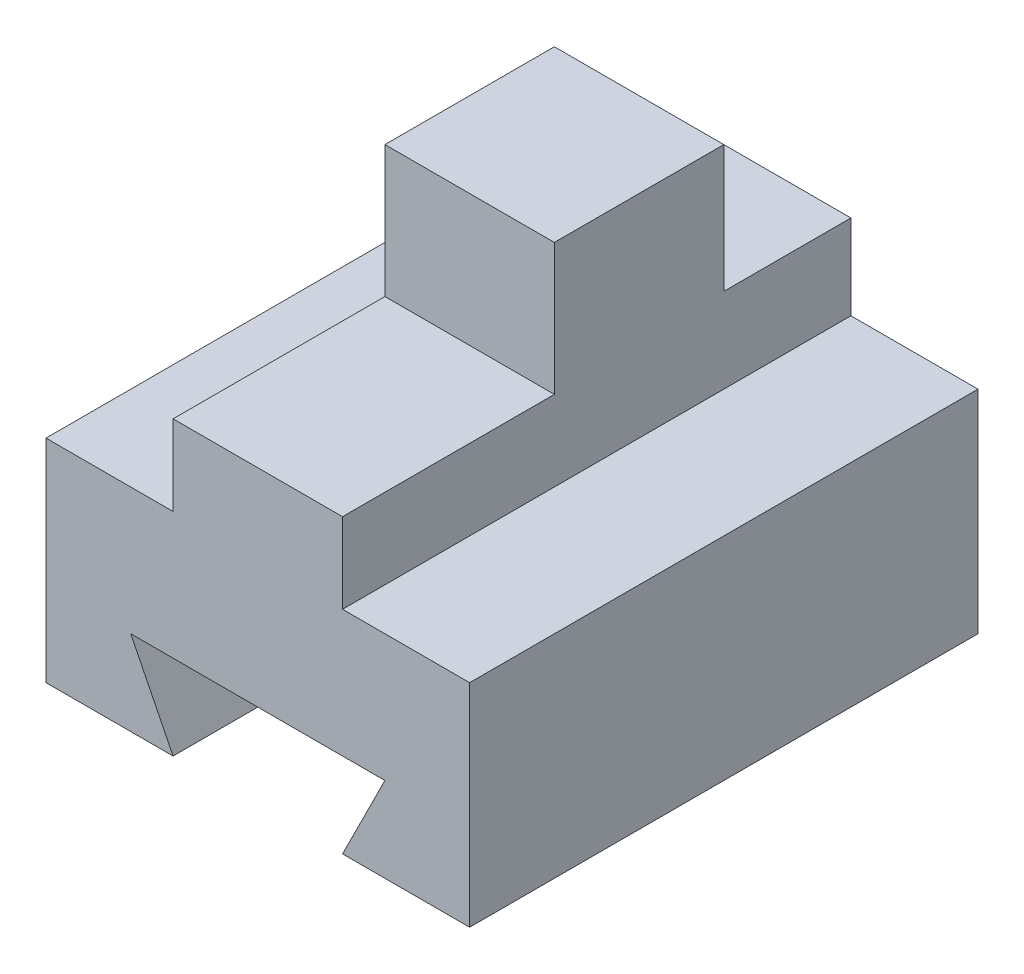
SolidWorks part; units mm, degrees
ref_plane "Ön Düzlem" through (0, 0, 0) normal (0, 0, 1) x (1, 0, 0)
ref_plane "Üst Düzlem" through (0, 0, 0) normal (0, 1, 0) x (1, 0, 0)
ref_plane "Sağ Düzlem" through (0, 0, 0) normal (1, 0, 0) x (0, 0, -1)
sketch "Çizim1" plane through (0, 0, 0) normal (0, 0, 1) x (1, 0, 0)
  line L1 (-38.103, 22.3684) -> (11.897, 22.3684)
  line L2 (-38.103, 22.3684) -> (-38.103, -27.6316)
  line L3 (-38.103, -27.6316) -> (11.897, -27.6316)
  line L4 (11.897, 22.3684) -> (11.897, -27.6316)
  dimension "D1" = 50
  dimension "D2" = 50
extrude "Yükseklik-Ekstrüzyon1" add sketch "Çizim1" along normal blind 60
sketch "Çizim2" plane through (0, 0, 60) normal (0, 0, 1) x (1, 0, 0)
  line L1 (-28.103, -17.6316) -> (1.897, -17.6316)
  line L2 (1.897, -17.6316) -> (-3.103, -27.6316)
  line L3 (-3.103, -27.6316) -> (-23.103, -27.6316)
  line L4 (-23.103, -27.6316) -> (-28.103, -17.6316)
extrude "Kes-Ekstrüzyon1" cut sketch "Çizim2" against normal blind 60
sketch "Çizim3" plane through (0, 0, 60) normal (0, 0, 1) x (1, 0, 0)
  line L1 (11.897, -27.6316) -> (11.897, 22.3684) construction
  line L2 (11.897, -2.6316) -> (-3.103, -2.6316)
  line L3 (-3.103, -2.6316) -> (-3.103, 22.3684)
  line L4 (11.897, 22.3684) -> (-38.103, 22.3684) construction
  line L5 (-3.103, 22.3684) -> (11.897, 22.3684)
  line L6 (11.897, 22.3684) -> (11.897, -2.6316)
  line L7 (-38.103, 22.3684) -> (-38.103, -27.6316) construction
  line L8 (-38.103, -2.6316) -> (-23.103, -2.6316)
  line L9 (-23.103, -2.6316) -> (-23.103, 22.3684)
  line L10 (-23.103, 22.3684) -> (-38.103, 22.3684)
  line L11 (-38.103, 22.3684) -> (-38.103, -2.6316)
  dimension "D2" = 15
extrude "Kes-Ekstrüzyon2" cut sketch "Çizim3" against normal blind 60
sketch "Çizim4" plane through (-23.103, 0, 0) normal (-1, 0, 0) x (0, 0, 1)
  line L1 (0, -2.6316) -> (0, 22.3684) construction
  line L2 (0, 7.3684) -> (15, 7.3684)
  line L3 (15, 7.3684) -> (15, 22.3684)
  line L4 (0, 22.3684) -> (60, 22.3684) construction
  line L6 (35, 22.3684) -> (35, 6.8364)
  line L7 (35, 6.8364) -> (60, 6.8364)
  line L8 (60, -2.6316) -> (60, 22.3684) construction
  line L9 (60, 6.8364) -> (60, 22.3684)
  line L10 (60, 22.3684) -> (35, 22.3684)
  line L11 (15, 22.3684) -> (0, 22.3684)
  line L12 (0, 22.3684) -> (0, 7.3684)
  dimension "D2" = 15
  dimension "D3" = 20
extrude "Kes-Ekstrüzyon3" cut sketch "Çizim4" against normal blind 20
